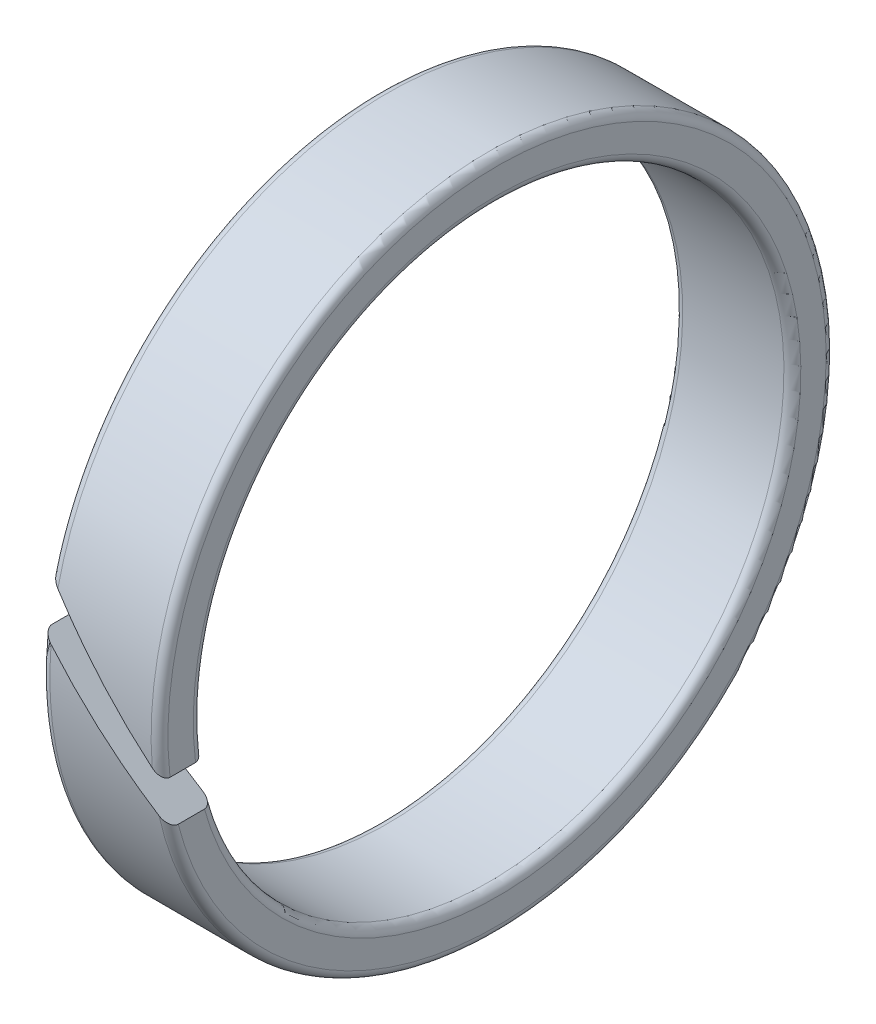
SolidWorks part; units mm, degrees
material "Фторопласт Ф4К15М5 ТУ 6-05-1413-76"
ref_plane "Plane1" through (0, 0, 0) normal (0, 0, 1) x (1, 0, 0)
ref_plane "Plane2" through (0, 0, 0) normal (0, 1, 0) x (1, 0, 0)
ref_plane "Plane3" through (0, 0, 0) normal (1, 0, 0) x (0, 0, -1)
sketch "Эскиз1" plane through (0, 0, 0) normal (0, 0, 1) x (1, 0, 0)
  line L1 (-2.8, 16) -> (2.8, 16)
  line L2 (-2.8, 16) -> (-2.8, 14)
  line L3 (-2.8, 14) -> (2.8, 14)
  line L4 (2.8, 16) -> (2.8, 14)
  line L5 (0, 0) -> (18.9412, 0) construction
  line L6 (0, 0) -> (0, 29.9353) construction
  dimension "D1" = 28
  dimension "D2" = 32
  dimension "D3" = 5.6
revolve "Повернуть1" add sketch "Эскиз1" angle 360 about L5
sketch "Эскиз2" plane through (0, 0, 0) normal (0, 0, 1) x (1, 0, 0)
  line L0 (2.8, -3.8607) -> (-3.8607, 2.8)
  line L1 (2.8, -3.8607) -> (3.8607, -2.8)
  line L2 (-3.8607, 2.8) -> (-2.8, 3.8607)
  line L3 (3.8607, -2.8) -> (-2.8, 3.8607)
  line L4 (2.8, -3.8607) -> (-2.8, 3.8607) construction
  line L5 (-3.8607, 2.8) -> (3.8607, -2.8) construction
  line L6 (0, 0) -> (9.2579, 0) construction
  line L7 (2.8, -16) -> (2.8, 16) construction
  point P1 (0, 0)
  dimension "D1" = 45
  dimension "D2" = 1.5
extrude "Вырез-Вытянуть1" cut sketch "Эскиз2" along normal through all
fillet "Скругление1" radius 0.4 4 edges at (-2.8, -2.8064, -15.752) (2.8, 2.8064, -15.752) (-2.8, -2.8084, -13.7154) (2.8, 2.8084, -13.7154)
